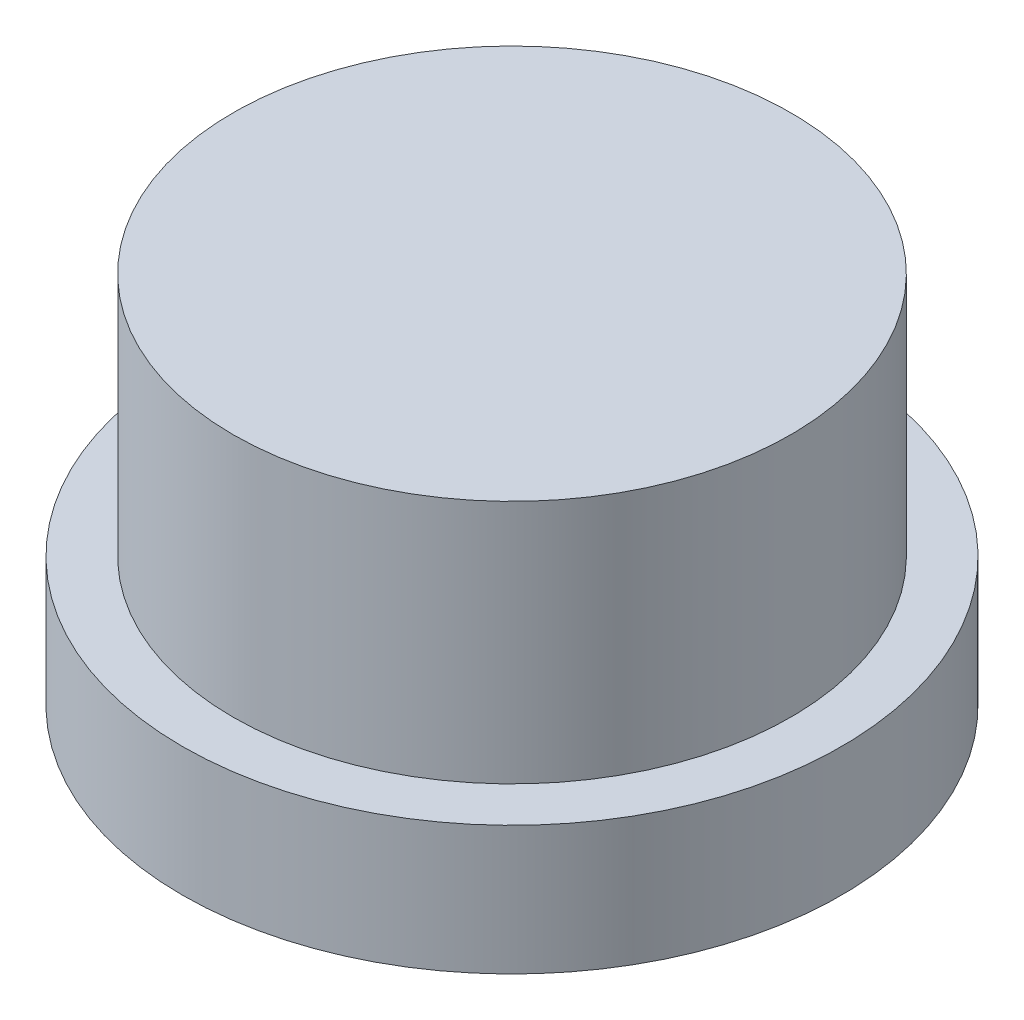
SolidWorks part; units mm, degrees
ref_plane "Front Plane" through (0, 0, 0) normal (0, 0, 1) x (1, 0, 0)
ref_plane "Top Plane" through (0, 0, 0) normal (0, 1, 0) x (1, 0, 0)
ref_plane "Right Plane" through (0, 0, 0) normal (1, 0, 0) x (0, 0, -1)
sketch "Sketch1" plane through (0, 0, 0) normal (0, 1, 0) x (1, 0, 0)
  circle A0 centre (0, 0) radius 6.5
extrude "Boss-Extrude1" add sketch "Sketch1" along normal blind 2.54
sketch "Sketch2" plane through (0, 2.54, 0) normal (0, 1, 0) x (1, 0, 0)
  circle A0 centre (0, 0) radius 5.5
extrude "Boss-Extrude2" add sketch "Sketch2" along normal blind 4.826
